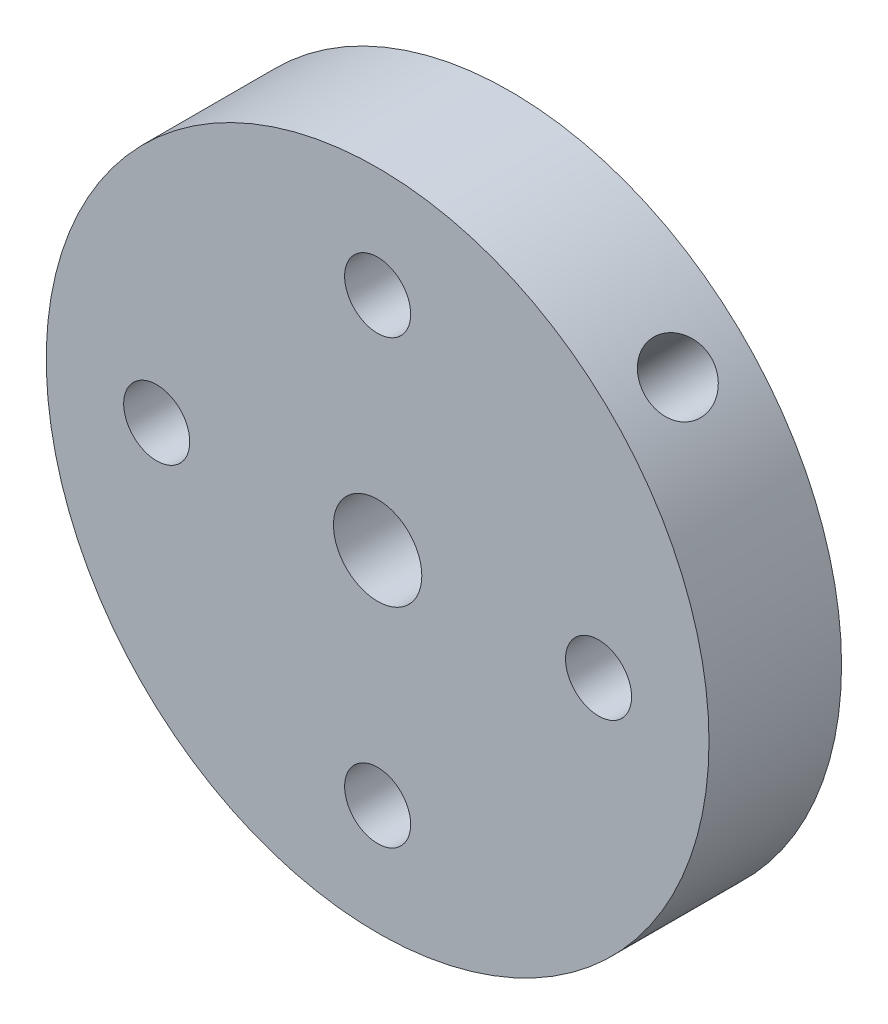
SolidWorks part; units mm, degrees
material "6061-T6 (SS)"
ref_plane "Front Plane" through (0, 0, 0) normal (0, 0, 1) x (1, 0, 0)
ref_plane "Top Plane" through (0, 0, 0) normal (0, 1, 0) x (1, 0, 0)
ref_plane "Right Plane" through (0, 0, 0) normal (1, 0, 0) x (0, 0, -1)
sketch "Sketch1" plane through (0, 0, 0) normal (0, 0, 1) x (1, 0, 0)
  circle A0 centre (0, 0) radius 19.05
  dimension "D1" = 38.1
extrude "Boss-Extrude1" add sketch "Sketch1" along normal blind 7.62
sketch "Sketch2" plane through (0, 0, 7.62) normal (0, 0, 1) x (1, 0, 0)
  circle A0 centre (0, 0) radius 2.54
  dimension "D1" = 5.08
extrude "Cut-Extrude1" cut sketch "Sketch2" against normal through all
sketch "Sketch4" plane through (0, 0, 7.62) normal (0, 0, 1) x (1, 0, 0)
  line L0 (0, 0) -> (0, 12.7) construction
  dimension "D1" = 12.7
hole_wizard "#10-24 Tapped Hole1" positions "Sketch6" profile "Sketch5" tap size "#10-24" standard "Ansi Inch" end condition through all
sketch "Sketch6" plane through (0, 0, 7.62) normal (0, 0, 1) x (1, 0, 0)
  point P1 (0, 12.7)
sketch "Sketch5" plane through (0, 12.7, 7.62) normal (1, 0, 0) x (0, -1, 0)
  line L0 (0, 0) -> (0, 7.62)
  line L1 (0, 7.62) -> (1.8986, 7.62)
  line L2 (1.8986, 7.62) -> (1.8986, 0)
  line L5 (1.8986, 0) -> (0, 0)
  line L11 (0, -6.35) -> (0, 107.95) construction
  dimension "Thru Tap Drill Dia." = 3.7973
  dimension "Thru Tap Drill Depth" = 7.62
cosmetic thread "Hole Thread1" parameters "D2"=4.826
pattern_circular "CirPattern1" count 4 over 360 about axis through (0, 0, 0) along (0, 0, 1) of "#10-24 Tapped Hole1"
sketch "Sketch7" plane through (0, 0, 7.62) normal (0, 0, 1) x (1, 0, 0)
  line L0 (0, 0) -> (13.4704, 13.4704) construction
  line L1 (0, 0) -> (0, 12.7) construction
  circle A0 centre (0, 0) radius 19.05 construction
  dimension "D1" = 45
ref_plane "Plane1" through (13.4704, 13.4704, 7.62) normal (0.7071, 0.7071, 0) x (-0.7071, 0.7071, 0)
sketch "Sketch8" plane through (13.4704, 13.4704, 7.62) normal (0.7071, 0.7071, 0) x (-0.7071, 0.7071, 0)
  line L0 (0, 0) -> (0, -7.62) construction
  point P4 (0, -3.81)
hole_wizard "#10-24 Tapped Hole4" positions "Sketch10" profile "Sketch9" tap size "#10-24" standard "Ansi Inch"
sketch "Sketch10" plane through (13.4704, 13.4704, 7.62) normal (0.7071, 0.7071, 0) x (-0.7071, 0.7071, 0)
  point P1 (0, -3.81)
sketch "Sketch9" plane through (13.4704, 13.4704, 3.81) normal (0, 0, 1) x (-0.7071, 0.7071, 0)
  line L0 (0, 0) -> (0, 21.1687)
  line L1 (0, 21.1687) -> (1.8986, 20.0279)
  line L2 (1.8986, 20.0279) -> (1.8986, 0)
  line L5 (1.8986, 0) -> (0, 0)
  line L10 (0, 21.1687) -> (-1.8987, 20.0279) construction
  line L11 (0, -6.35) -> (0, 107.95) construction
  dimension "Tap Drill Dia." = 3.7973
  dimension "Tap Drill Depth" = 20.0279
  dimension "Drill Angle" = 118
cosmetic thread "Hole Thread2" parameters "D1"=9.652, "D2"=4.826
